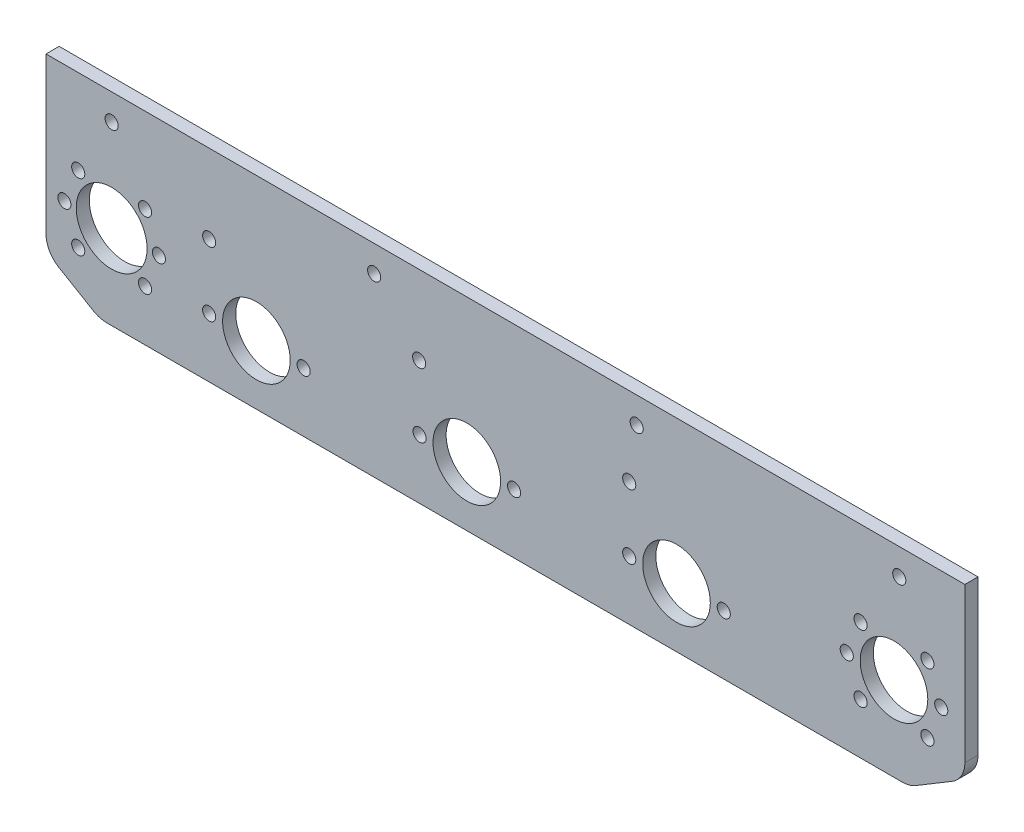
SolidWorks part; units mm, degrees
ref_plane "前基準面" through (0, 0, 0) normal (0, 0, 1) x (1, 0, 0)
ref_plane "上基準面" through (0, 0, 0) normal (0, 1, 0) x (1, 0, 0)
ref_plane "右基準面" through (0, 0, 0) normal (1, 0, 0) x (0, 0, -1)
sketch "草圖1" plane through (0, 0, 0) normal (0, 0, 1) x (1, 0, 0)
  line L0 (-174, 47.428) -> (176, 47.428) construction
  line L1 (-174, 57.428) -> (176, 57.428)
  line L2 (-174, 57.428) -> (-174, 7.6125)
  line L3 (176, 57.428) -> (176, 7.6125)
  line L4 (131, 57.428) -> (131, -34.0563) construction
  line L5 (131, 12.428) -> (167, 12.428) construction
  line L6 (-174, 37.428) -> (176, 37.428) construction
  line L7 (-149, 12.428) -> (-149, 25.928) construction
  line L8 (-162.5972, 25.928) -> (-135.5, 25.928) construction
  line L9 (-162.5972, 25.928) -> (-162.5972, -1.1692) construction
  line L10 (-162.5972, -1.1692) -> (-135.5, -1.1692) construction
  line L11 (-135.5, 25.928) -> (-135.5, -1.1692) construction
  line L12 (-162.5972, 25.928) -> (-135.5, -1.1692) construction
  line L13 (-162.5972, -1.1692) -> (-135.5, 25.928) construction
  line L14 (-149, 12.428) -> (-162.5, 12.428) construction
  line L15 (-111.8548, 57.428) -> (-111.8548, -47.572) construction
  line L16 (116, 57.428) -> (116, -43.0612) construction
  line L17 (-119, 27.428) -> (119, 27.428) construction
  line L18 (-149, 12.428) -> (-93.8574, 12.428) construction
  line L19 (-93.8574, 12.428) -> (-93.8574, 2.8852) construction
  line L20 (-93.8574, 2.8852) -> (-75.8574, 2.8852) construction
  line L21 (-93.8574, 2.8852) -> (95.7208, 2.8852) construction
  line L22 (-174, 0.5231) -> (-174, -1.9427)
  line L23 (-174, 7.6125) -> (-174, 0.5231)
  line L24 (176, -1.3815) -> (176, 7.6125)
  line L25 (-169.0826, -10.5547) -> (-155.9229, -18.3213)
  line L26 (-150.8403, -19.7093) -> (152.1278, -19.7093)
  line L27 (157.2748, -18.283) -> (171.147, -9.9552)
  line L28 (0, 92.6571) -> (0, -92.6571) construction
  line L29 (-149, 42.428) -> (192.2963, 42.428) construction
  line L30 (-31.8548, 27.428) -> (-31.8548, -13.7488) construction
  line L31 (48.1452, 27.428) -> (48.1452, -17.074) construction
  circle A0 centre (131, 12.428) radius 2.5
  circle A1 centre (167, 12.428) radius 2.5
  circle A2 centre (149, 12.428) radius 12.875
  circle A3 centre (149, 12.428) radius 30 construction
  circle A4 centre (-149, 12.428) radius 13.5
  circle A5 centre (-136.2721, 25.1559) radius 2.5
  circle A6 centre (-161.7279, 25.1559) radius 2.5
  circle A7 centre (-136.2721, -0.2999) radius 2.5
  circle A8 centre (-161.7279, -0.2999) radius 2.5
  circle A9 centre (-149, 12.428) radius 30 construction
  circle A10 centre (-111.8548, 27.428) radius 2.5
  circle A11 centre (-31.8548, 27.428) radius 2.5
  circle A12 centre (48.1452, 27.428) radius 2.5
  circle A13 centre (-93.8574, 2.8852) radius 12.875
  circle A14 centre (-75.8574, 2.8852) radius 2.5
  circle A15 centre (-111.8574, 2.8852) radius 2.5
  circle A16 centre (-31.7164, 2.9555) radius 2.5
  circle A17 centre (-13.7164, 2.9555) radius 12.875
  circle A18 centre (4.2836, 2.9555) radius 2.5
  circle A19 centre (48.1587, 2.8777) radius 2.5
  circle A20 centre (66.1587, 2.8777) radius 12.875
  circle A21 centre (84.1587, 2.8777) radius 2.5
  circle A22 centre (-149, 47.428) radius 2.5
  circle A23 centre (-49, 47.428) radius 2.5
  circle A24 centre (51, 47.428) radius 2.5
  circle A25 centre (151, 47.428) radius 2.5
  circle A26 centre (-93.8574, 2.8852) radius 30 construction
  arc A27 (-155.9229, -18.3213) -> (-150.8403, -19.7093) centre (-150.8403, -9.7093) ccw
  arc A28 (-169.0826, -10.5547) -> (-174, -1.9427) centre (-164, -1.9427) cw
  arc A29 (171.147, -9.9552) -> (176, -1.3815) centre (166, -1.3815) ccw
  arc A30 (157.2748, -18.283) -> (152.1278, -19.7093) centre (152.1278, -9.7093) cw
  circle A31 centre (-167, 12.428) radius 2.5
  circle A32 centre (-131, 12.428) radius 2.5
  circle A33 centre (161.7279, -0.2999) radius 2.5
  circle A34 centre (136.2721, -0.2999) radius 2.5
  circle A35 centre (136.2721, 25.1559) radius 2.5
  circle A36 centre (161.7279, 25.1559) radius 2.5
  point P0 (3.4028, 10.8308)
  dimension "D4" = 5
  dimension "D8" = 60
  dimension "D9" = 27
  dimension "D18" = 25.75
  dimension "D19" = 25.75
  dimension "D20" = 60
  dimension "D21" = 60
  dimension "D22" = 10
  dimension "D23" = 10
  dimension "D1" = 350
  dimension "D2" = 10
  dimension "D3" = 45
  dimension "D5" = 45
  dimension "D6" = 36
  dimension "D7" = 20
  dimension "D10" = 25
  dimension "D11" = 45
  dimension "D12" = 18
  dimension "D13" = 15
  dimension "D14" = 62.1452
  dimension "D15" = 60
  dimension "D16" = 80
  dimension "D17" = 80
  dimension "D24" = 17.9974
  dimension "D25" = 18
  dimension "D26" = 149
extrude "填料-伸長1" add sketch "草圖1" along normal blind 5
